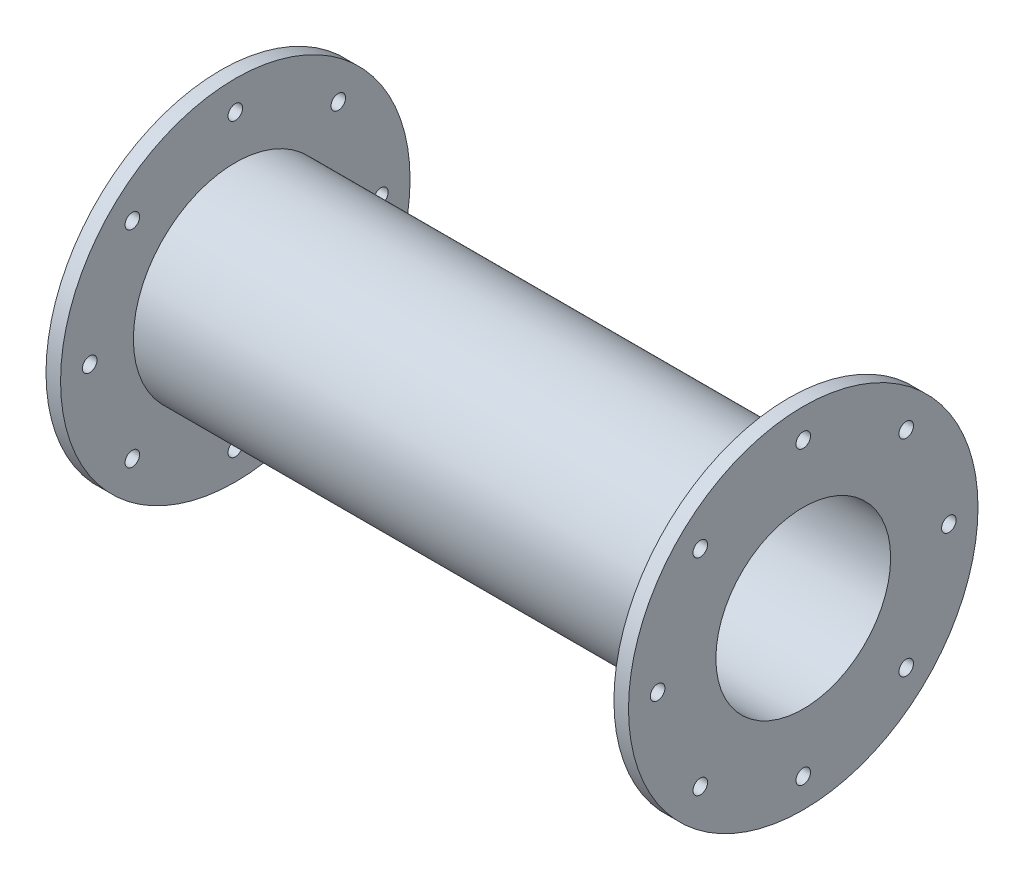
SolidWorks part; units mm, degrees
ref_plane "Front Plane" through (0, 0, 0) normal (0, 0, 1) x (1, 0, 0)
ref_plane "Top Plane" through (0, 0, 0) normal (0, 1, 0) x (1, 0, 0)
ref_plane "Right Plane" through (0, 0, 0) normal (1, 0, 0) x (0, 0, -1)
ref_axis "Axis1" through (-152.49, 0, 0) along (1, 0, 0)
sketch "Sketch1" plane through (0, 0, 0) normal (0, 0, 1) x (1, 0, 0)
  line L0 (0, 38.1) -> (0, 19.05)
  line L1 (0, 19.05) -> (-127, 19.05)
  line L2 (-127, 19.05) -> (-127, 38.1)
  line L3 (-127, 38.1) -> (-123.825, 38.1)
  line L4 (-123.825, 38.1) -> (-123.825, 22.225)
  line L5 (-123.825, 22.225) -> (-3.175, 22.225)
  line L6 (-3.175, 22.225) -> (-3.175, 38.1)
  line L7 (-3.175, 38.1) -> (0, 38.1)
  dimension "D1" = 19.05
  dimension "D2" = 3.175
  dimension "D3" = 3.175
  dimension "D4" = 38.1
  dimension "D5" = 127
  dimension "D6" = 3.175
  dimension "D7" = 38.1
revolve "Revolve1" add sketch "Sketch1" angle 360 about axis through (-152.49, 0, 0) along (1, 0, 0)
hole_wizard "1/8 (0.125) Diameter Hole1" positions "Sketch2" profile "Sketch3" hole size "1/8" standard "ANSI Inch" end condition through all
sketch "Sketch2" plane through (0, 0, 0) normal (1, 0, 0) x (0, 0, -1)
  point P0 (0, 31.75)
  dimension "D1" = 31.75
sketch "Sketch3" plane through (0, 31.75, 0) normal (0, 1, 0) x (0, 0, -1)
  line L0 (0, 0) -> (0, 127)
  line L1 (0, 127) -> (1.5875, 127)
  line L2 (1.5875, 127) -> (1.5875, 0)
  line L5 (1.5875, 0) -> (0, 0)
  line L11 (0, -6.35) -> (0, 107.95) construction
  dimension "Thru Hole Dia." = 3.175
  dimension "Thru Hole Depth" = 127
pattern_circular "CirPattern1" count 8 over 360 about axis through (0, 0, 0) along (1, 0, 0) of "1/8 (0.125) Diameter Hole1"
